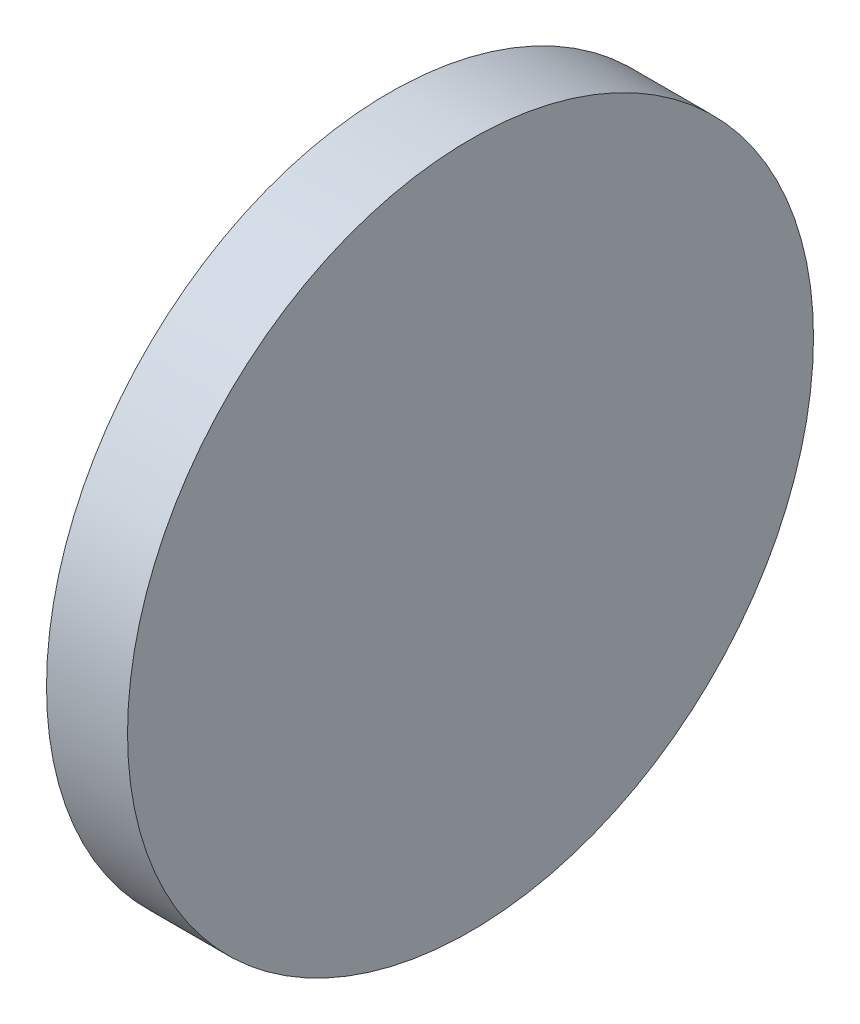
SolidWorks part; units mm, degrees
ref_plane "前视基准面" through (0, 0, 0) normal (0, 0, 1) x (1, 0, 0)
ref_plane "上视基准面" through (0, 0, 0) normal (0, 1, 0) x (1, 0, 0)
ref_plane "右视基准面" through (0, 0, 0) normal (1, 0, 0) x (0, 0, -1)
sketch "草图1" plane through (0, 0, 0) normal (0, 0, 1) x (1, 0, 0)
  line L0 (-3, 19.05) -> (-3, 0)
  line L2 (-3, 19.05) -> (3, 19.05)
  line L3 (-3, 0) -> (3, 0)
  line L4 (3, 19.05) -> (3, 0)
revolve "旋转2" add sketch "草图1" angle 360 about L3
sketch "草图4" plane through (0, 0, 0) normal (0, 0, 1) x (1, 0, 0)
  line L0 (-3, 25.4) -> (3, 25.4)
  line L1 (3, 25.4) -> (3, 19.05)
  line L2 (3, 19.05) -> (-3, 19.05)
  line L3 (3, 19.05) -> (-3, 19.05) construction
  line L4 (-3, 19.05) -> (-3, 25.4)
  line L5 (0, 19.05) -> (0, 25.4) construction
  line L6 (-1.6142, 0) -> (1.5903, 0) construction
revolve "旋转3" add sketch "草图4" angle 360 about L6
equation "\"D1@草图4\"=\"D1@草图1\""
